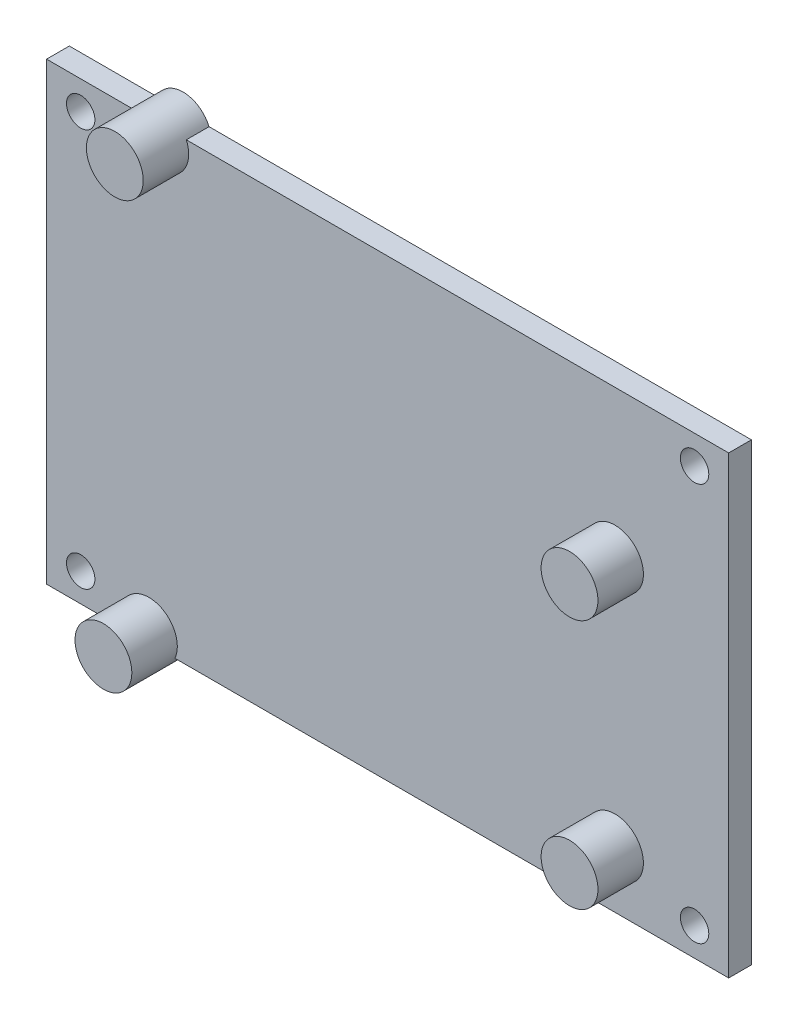
SolidWorks part; units mm, degrees
ref_plane "Front Plane" through (0, 0, 0) normal (0, 0, 1) x (1, 0, 0)
ref_plane "Top Plane" through (0, 0, 0) normal (0, 1, 0) x (1, 0, 0)
ref_plane "Right Plane" through (0, 0, 0) normal (1, 0, 0) x (0, 0, -1)
sketch "Sketch1" plane through (0, 0, 0) normal (0, 0, 1) x (1, 0, 0)
  line L1 (-38.1, -25.4) -> (38.1, -25.4)
  line L2 (-38.1, -25.4) -> (-38.1, 25.4)
  line L3 (-38.1, 25.4) -> (38.1, 25.4)
  line L4 (38.1, -25.4) -> (38.1, 25.4)
  line L5 (-38.1, -25.4) -> (38.1, 25.4) construction
  line L6 (-38.1, 25.4) -> (38.1, -25.4) construction
  circle A0 centre (-34.29, 22.225) radius 1.5875
  circle A1 centre (34.29, 22.225) radius 1.5875
  circle A2 centre (34.29, -22.225) radius 1.5875
  circle A3 centre (-34.29, -22.225) radius 1.5875
  point P0 (0, 0)
  dimension "D3" = 3.175
  dimension "D4" = 3.175
  dimension "D5" = 3.81
  dimension "D6" = 2
  dimension "D1" = 50.8
  dimension "D2" = 76.2
  dimension "D7" = 2
extrude "Boss-Extrude1" add sketch "Sketch1" along normal blind 2.54
sketch "Sketch2" plane through (0, 0, 2.54) normal (0, 0, 1) x (1, 0, 0)
  line L0 (38.1, 25.4) -> (-38.1, 25.4) construction
  line L1 (-38.1, 25.4) -> (-38.1, -25.4) construction
  circle A0 centre (-25.4, 24.13) radius 3.175
  circle A1 centre (-26.67, -24.13) radius 3.175
  circle A2 centre (25.4, 8.89) radius 3.175
  circle A3 centre (25.4, -19.05) radius 3.175
  dimension "D1" = 6.35
  dimension "D4" = 6.35
  dimension "D8" = 6.35
  dimension "D9" = 6.35
  dimension "D2" = 48.26
  dimension "D3" = 1.27
  dimension "D5" = 1.27
  dimension "D6" = 15.24
  dimension "D7" = 27.94
  dimension "D10" = 50.8
  dimension "D11" = 12.7
extrude "Boss-Extrude2" add sketch "Sketch2" along normal blind 5.08 and the other way blind 2.54
